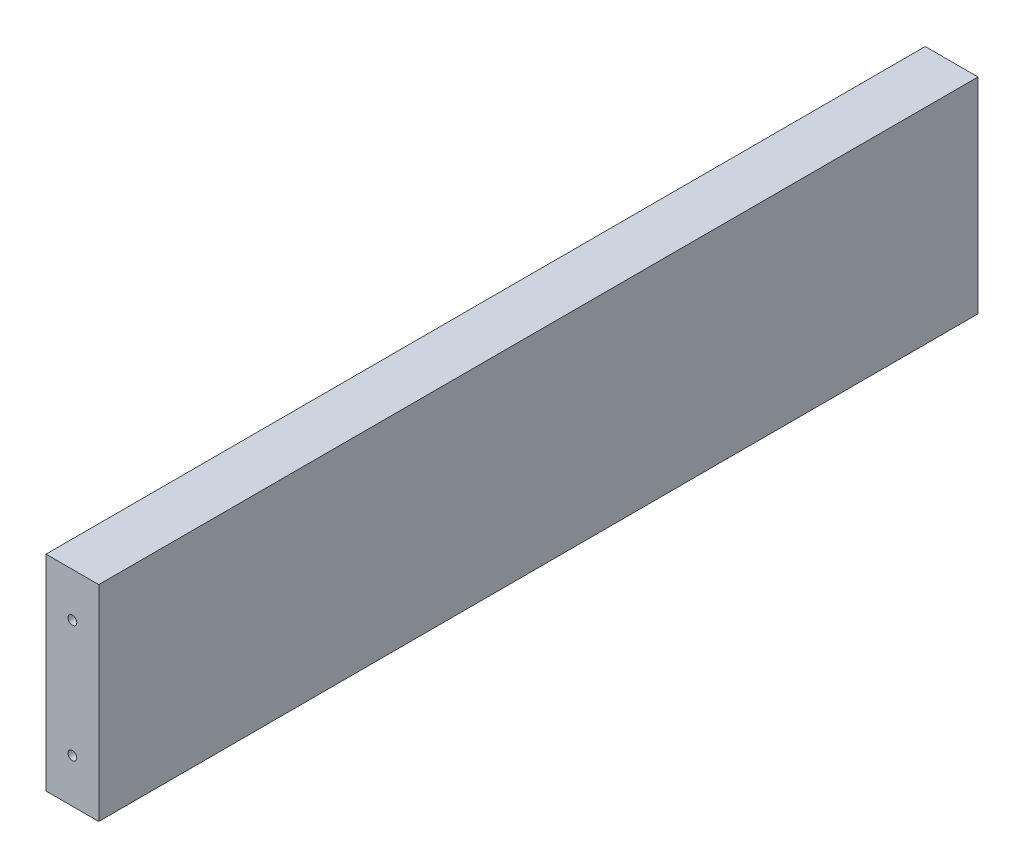
SolidWorks part; units mm, degrees
material "Bronce de aluminio"
ref_plane "Front Plane" through (0, 0, 0) normal (0, 0, 1) x (1, 0, 0)
ref_plane "Top Plane" through (0, 0, 0) normal (0, 1, 0) x (1, 0, 0)
ref_plane "Right Plane" through (0, 0, 0) normal (1, 0, 0) x (0, 0, -1)
sketch "Croquis1" plane through (0, 0, 0) normal (0, 0, 1) x (1, 0, 0)
  line L0 (0, 0) -> (0, 25) construction
  line L1 (150, -35) -> (-150, -35)
  line L2 (150, -35) -> (150, 35)
  line L3 (150, 35) -> (-150, 35)
  line L4 (-150, -35) -> (-150, 35)
  line L5 (150, -35) -> (-150, 35) construction
  line L6 (150, 35) -> (-150, -35) construction
  line L7 (141, -20) -> (141, 20) construction
  line L8 (-150, 0) -> (-141, 0) construction
  line L9 (90, 25) -> (-90, 25) construction
  line L10 (-33.333, 25) -> (0, 25) construction
  line L11 (0, 25) -> (0, -8.333) construction
  line L12 (0, 25) -> (33.333, 25) construction
  line L13 (150, 0) -> (141, 0) construction
  line L14 (-141, -20) -> (-141, 20) construction
  line L15 (-33.333, 25) -> (0, -8.333) construction
  line L16 (0, -8.333) -> (33.333, 25) construction
  circle A0 centre (0, 25) radius 11
  circle A1 centre (90, 25) radius 4
  circle A2 centre (-90, 25) radius 4
  circle A3 centre (-33.333, 25) radius 2.85
  circle A4 centre (33.333, 25) radius 2.85
  circle A5 centre (0, -8.333) radius 2.85
  circle A6 centre (-141, 20) radius 1.5
  circle A7 centre (-141, -20) radius 1.5
  circle A8 centre (141, 20) radius 1.5
  circle A9 centre (141, -20) radius 1.5
  point P0 (0, 0)
  point P14 (0, 25)
  point P25 (141, 0)
  point P30 (-141, 0)
  dimension "D3" = 22
  dimension "D6" = 8
  dimension "D7" = 47.14
  dimension "D8" = 5.7
  dimension "D11" = 3
  dimension "D1" = 300
  dimension "D2" = 70
  dimension "D4" = 60
  dimension "D5" = 180
  dimension "D9" = 9
  dimension "D10" = 40
sketch "Croquis2" plane through (0, 0, 0) normal (0, 0, 1) x (1, 0, 0)
  line L0 (150, -35) -> (150, 35) construction
  line L1 (150, -35) -> (-150, -35) construction
  line L2 (150, 35) -> (-150, 35) construction
  line L3 (-150, -35) -> (-150, 35) construction
  line L4 (150, -35) -> (150, 35)
  line L5 (150, -35) -> (-150, -35)
  line L6 (150, 35) -> (-150, 35)
  line L7 (-150, -35) -> (-150, 35)
  circle A0 centre (-141, -20) radius 1.5 construction
  circle A1 centre (-141, 20) radius 1.5 construction
  circle A2 centre (141, -20) radius 1.5 construction
  circle A3 centre (141, 20) radius 1.5 construction
  circle A4 centre (90, 25) radius 4 construction
  circle A5 centre (0, 25) radius 11 construction
  circle A6 centre (-90, 25) radius 4 construction
  circle A7 centre (-141, -20) radius 1.5
  circle A8 centre (-141, 20) radius 1.5
  circle A9 centre (141, -20) radius 1.5
  circle A10 centre (141, 20) radius 1.5
  circle A11 centre (90, 25) radius 4
  circle A12 centre (0, 25) radius 11
  circle A13 centre (-90, 25) radius 4
  circle A14 centre (0, -8.333) radius 2.85 construction
  circle A15 centre (33.333, 25) radius 2.85 construction
  circle A16 centre (-33.333, 25) radius 2.85 construction
  circle A17 centre (0, -8.333) radius 2.85
  circle A18 centre (33.333, 25) radius 2.85
  circle A19 centre (-33.333, 25) radius 2.85
extrude "Saliente-Extruir1" [suppressed] add sketch "Croquis2" along normal blind 18 contours A12 L6 L7 L5 L4 A13 A11 A10 A9 A8 A7
sketch "Croquis3" plane through (0, 0, 0) normal (0, 0, 1) x (1, 0, 0)
  line L0 (150, -35) -> (150, 35) construction
  line L1 (150, 35) -> (-150, 35) construction
  line L2 (150, -35) -> (-150, -35) construction
  line L3 (-150, -35) -> (-150, 35) construction
  line L4 (150, -35) -> (150, 35)
  line L5 (150, 35) -> (-150, 35)
  line L6 (150, -35) -> (-150, -35)
  line L7 (-150, -35) -> (-150, 35)
  circle A0 centre (-90, 25) radius 4 construction
  circle A1 centre (-141, -20) radius 1.5 construction
  circle A2 centre (-141, 20) radius 1.5 construction
  circle A3 centre (141, -20) radius 1.5 construction
  circle A4 centre (141, 20) radius 1.5 construction
  circle A5 centre (90, 25) radius 4 construction
  circle A6 centre (0, 25) radius 11 construction
  circle A7 centre (-90, 25) radius 4
  circle A8 centre (-141, -20) radius 1.5
  circle A9 centre (-141, 20) radius 1.5
  circle A10 centre (141, -20) radius 1.5
  circle A11 centre (141, 20) radius 1.5
  circle A12 centre (90, 25) radius 4
  circle A13 centre (0, 25) radius 11
extrude "Saliente-Extruir2" [suppressed] add sketch "Croquis3" along normal blind 9 contours A13 L5 L7 L6 L4 A12 A11 A10 A9 A8 A7
sketch "Croquis6" plane through (0, 0, 0) normal (0, 0, 1) x (1, 0, 0)
  line L0 (150, -35) -> (150, 35) construction
  line L1 (150, -35) -> (-150, -35) construction
  line L2 (150, 35) -> (-150, 35) construction
  line L3 (-150, -35) -> (-150, 35) construction
  line L4 (150, -35) -> (150, 35)
  line L5 (150, -35) -> (-150, -35)
  line L6 (150, 35) -> (-150, 35)
  line L7 (-150, -35) -> (-150, 35)
  circle A0 centre (90, 25) radius 4 construction
  circle A1 centre (-90, 25) radius 4 construction
  circle A2 centre (-141, -20) radius 1.5 construction
  circle A3 centre (90, 25) radius 4
  circle A4 centre (-90, 25) radius 4
  circle A5 centre (-141, -20) radius 1.5
  circle A6 centre (141, -20) radius 1.5 construction
  circle A7 centre (141, 20) radius 1.5 construction
  circle A8 centre (-141, 20) radius 1.5 construction
  circle A9 centre (141, -20) radius 1.5
  circle A10 centre (141, 20) radius 1.5
  circle A11 centre (-141, 20) radius 1.5
  circle A12 centre (0, 25) radius 4
  point P0 (141, -20)
  point P2 (141, 20)
  point P4 (-141, 20)
  dimension "D1" = 8
extrude "Saliente-Extruir3" [suppressed] add sketch "Croquis6" against normal blind 9
ref_plane "Plano1" through (-150, 0, 0) normal (1, 0, 0) x (0, 0, -1)
sketch "Croquis7" plane through (-150, 0, 0) normal (1, 0, 0) x (0, 0, -1)
  line L0 (150, 0) -> (115, 0) construction
  line L1 (-150, -35) -> (150, -35)
  line L2 (-150, -35) -> (-150, 35)
  line L3 (-150, 35) -> (150, 35)
  line L4 (150, -35) -> (150, 35)
  line L5 (-150, -35) -> (150, 35) construction
  line L6 (-150, 35) -> (150, -35) construction
  line L8 (140, -7.5) -> (90, -7.5) construction
  line L9 (140, -7.5) -> (140, 7.5) construction
  line L10 (140, 7.5) -> (90, 7.5) construction
  line L11 (90, -7.5) -> (90, 7.5) construction
  line L12 (140, -7.5) -> (90, 7.5) construction
  line L13 (140, 7.5) -> (90, -7.5) construction
  circle A0 centre (90, 7.5) radius 1.5
  circle A1 centre (140, 7.5) radius 1.5
  circle A2 centre (90, -7.5) radius 1.5
  circle A3 centre (140, -7.5) radius 1.5
  point P0 (0, 0)
  dimension "D6" = 3
  dimension "D1" = 300
  dimension "D2" = 70
  dimension "D3" = 35
  dimension "D4" = 50
  dimension "D5" = 15
extrude "Saliente-Extruir4" add sketch "Croquis7" along normal blind 18
sketch "Croquis8" plane through (0, 0, 150) normal (0, 0, 1) x (1, 0, 0)
  circle A0 centre (-141, -20) radius 1.5 construction
  circle A1 centre (-141, 20) radius 1.5 construction
  circle A2 centre (-141, -20) radius 1.5
  circle A3 centre (-141, 20) radius 1.5
extrude "Cortar-Extruir1" cut sketch "Croquis8" against normal blind 12
sketch "Croquis9" plane through (0, 0, -150) normal (0, 0, -1) x (-1, 0, 0)
  circle A0 centre (141, -20) radius 1.5 construction
  circle A1 centre (141, 20) radius 1.5 construction
  circle A2 centre (141, -20) radius 1.5
  circle A3 centre (141, 20) radius 1.5
extrude "Cortar-Extruir2" cut sketch "Croquis9" against normal blind 12
sketch "Croquis10" [suppressed] plane through (0, 0, 0) normal (0, 0, 1) x (1, 0, 0)
  circle A0 centre (-90, 25) radius 4 construction
  circle A1 centre (-90, 25) radius 4
extrude "Saliente-Extruir5" [suppressed] add sketch "Croquis10" along normal blind 400
sketch "Croquis11" [suppressed] plane through (0, 0, 0) normal (0, 1, 0) x (1, 0, 0)
  line L0 (0, 0) -> (-90, 0) construction
  line L1 (125, -75) -> (-125, -75)
  line L2 (125, -75) -> (125, 75)
  line L3 (125, 75) -> (-125, 75)
  line L4 (-125, -75) -> (-125, 75)
  line L5 (125, -75) -> (-125, 75) construction
  line L6 (125, 75) -> (-125, -75) construction
  line L7 (17.5, -11.25) -> (-17.5, -11.25) construction
  line L8 (17.5, -11.25) -> (17.5, 11.25) construction
  line L9 (17.5, 11.25) -> (-17.5, 11.25) construction
  line L10 (-17.5, -11.25) -> (-17.5, 11.25) construction
  line L11 (17.5, -11.25) -> (-17.5, 11.25) construction
  line L12 (17.5, 11.25) -> (-17.5, -11.25) construction
  line L13 (-90, 0) -> (-90, 50) construction
  line L14 (-115, 65) -> (-115, -35) construction
  line L15 (-65, 35) -> (-115, 35) construction
  line L16 (-65, 35) -> (-65, 65) construction
  line L17 (-65, 65) -> (-115, 65) construction
  line L18 (-115, 35) -> (-115, 65) construction
  line L19 (-65, 35) -> (-115, 65) construction
  line L20 (-65, 65) -> (-115, 35) construction
  circle A0 centre (-115, 65) radius 2.5
  circle A1 centre (-65, 65) radius 2.5
  circle A2 centre (-115, 35) radius 2.5
  circle A3 centre (-65, 35) radius 2.5
  circle A4 centre (65, 65) radius 2.5
  circle A5 centre (115, 65) radius 2.5
  circle A6 centre (65, 35) radius 2.5
  circle A7 centre (115, 35) radius 2.5
  circle A8 centre (-115, -35) radius 2.5
  circle A9 centre (-115, -65) radius 2.5
  circle A10 centre (-65, -65) radius 2.5
  circle A11 centre (-65, -35) radius 2.5
  circle A12 centre (65, -35) radius 2.5
  circle A13 centre (65, -65) radius 2.5
  circle A14 centre (115, -35) radius 2.5
  circle A15 centre (115, -65) radius 2.5
  circle A16 centre (-17.5, 11.25) radius 2.5
  circle A17 centre (17.5, 11.25) radius 2.5
  circle A18 centre (-17.5, -11.25) radius 2.5
  circle A19 centre (17.5, -11.25) radius 2.5
  point P0 (0, 0)
  point P6 (0, 0)
  dimension "D8" = 5
  dimension "D1" = 250
  dimension "D2" = 150
  dimension "D3" = 35
  dimension "D4" = 22.5
  dimension "D5" = 90
  dimension "D6" = 50
  dimension "D7" = 30
  dimension "D10" = 130
  dimension "D12" = 100
  dimension "D13" = 50
  dimension "D9" = 2
  dimension "D11" = 2
extrude "Saliente-Extruir6" [suppressed] add sketch "Croquis11" against normal blind 17
sketch "Croquis12" [suppressed] plane through (0, 0, 0) normal (0, 1, 0) x (1, 0, 0)
  line L0 (-125, -75) -> (125, -75) construction
  line L1 (125, -75) -> (125, 75) construction
  line L2 (125, 75) -> (-125, 75) construction
  line L3 (-125, 75) -> (-125, -75) construction
  line L4 (-125, -75) -> (125, -75)
  line L5 (125, -75) -> (125, 75)
  line L6 (125, 75) -> (-125, 75)
  line L7 (-125, 75) -> (-125, -75)
extrude "Saliente-Extruir7" [suppressed] add sketch "Croquis12" along normal blind 1
sketch "Croquis13" plane through (-150, 0, 0) normal (-1, 0, 0) x (0, 0, 1)
  circle A0 centre (-90, 7.5) radius 1.5 construction
  circle A1 centre (-90, -7.5) radius 1.5 construction
  circle A2 centre (-140, -7.5) radius 1.5 construction
  circle A3 centre (-140, 7.5) radius 1.5 construction
  circle A4 centre (-90, 7.5) radius 1.5
  circle A5 centre (-90, -7.5) radius 1.5
  circle A6 centre (-140, -7.5) radius 1.5
  circle A7 centre (-140, 7.5) radius 1.5
extrude "Saliente-Extruir8" [suppressed] add sketch "Croquis13" against normal blind 12
sketch "Croquis14" plane through (-132, 0, 0) normal (1, 0, 0) x (0, 0, -1)
  circle A0 centre (140, -7.5) radius 1.5 construction
  circle A1 centre (140, 7.5) radius 1.5 construction
  circle A2 centre (90, -7.5) radius 1.5 construction
  circle A3 centre (90, 7.5) radius 1.5 construction
  circle A4 centre (140, -7.5) radius 1.5
  circle A5 centre (140, 7.5) radius 1.5
  circle A6 centre (90, -7.5) radius 1.5
  circle A7 centre (90, 7.5) radius 1.5
extrude "Saliente-Extruir9" add sketch "Croquis14" against normal blind 12
